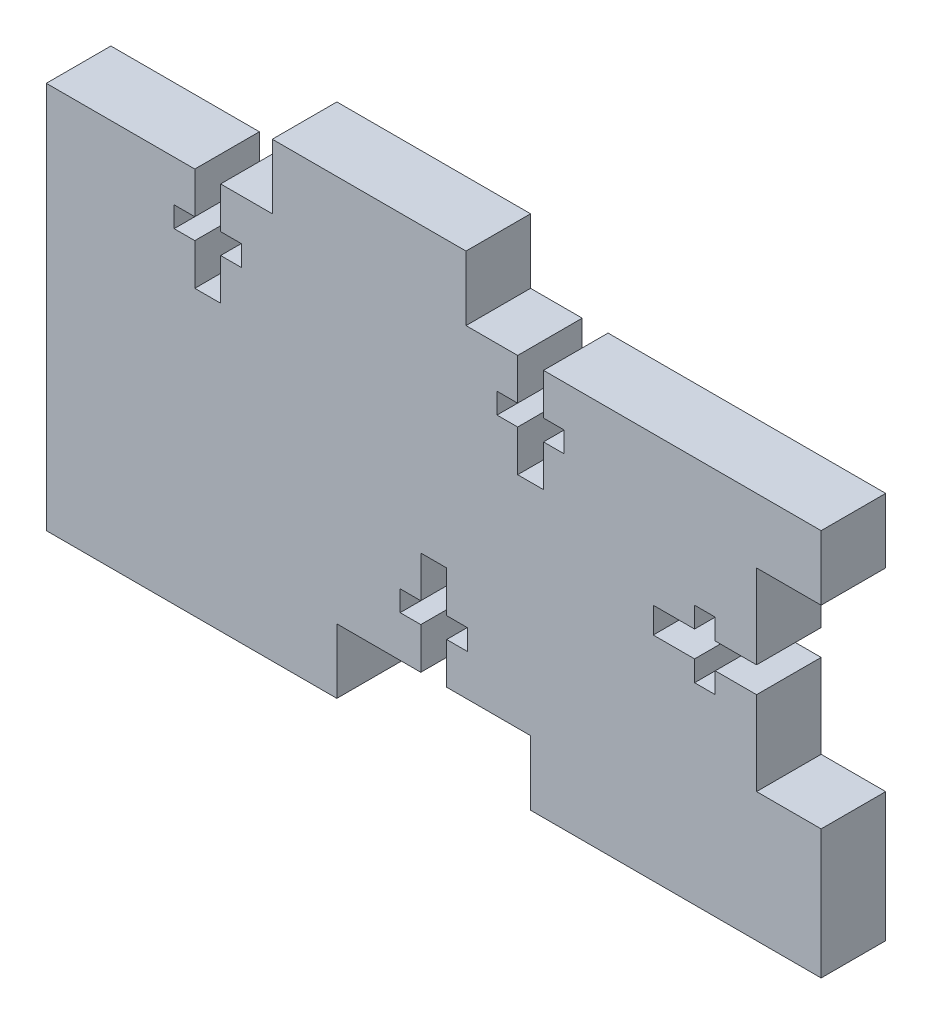
SolidWorks part; units mm, degrees
ref_plane "Front" through (0, 0, 0) normal (0, 0, 1) x (1, 0, 0)
ref_plane "Top" through (0, 0, 0) normal (0, 1, 0) x (1, 0, 0)
ref_plane "Right" through (0, 0, 0) normal (1, 0, 0) x (0, 0, -1)
sketch "Sketch1" plane through (0, 0, 0) normal (0, 0, 1) x (1, 0, 0)
  line L1 (-38.1, -15.875) -> (38.1, -15.875)
  line L2 (-38.1, -15.875) -> (-38.1, 15.875)
  line L3 (-38.1, 15.875) -> (38.1, 15.875)
  line L4 (38.1, -15.875) -> (38.1, 15.875)
  line L5 (-38.1, -15.875) -> (38.1, 15.875) construction
  line L6 (-38.1, 15.875) -> (38.1, -15.875) construction
  point P0 (0, 0)
  dimension "D1" = 31.75
  dimension "D2" = 76.2
extrude "Boss-Extrude1" add sketch "Sketch1" along normal blind 6.35
sketch "Sketch2" plane through (0, 0, 6.35) normal (0, 0, 1) x (1, 0, 0)
  line L0 (-38.1, 15.875) -> (-38.1, -15.875) construction
  line L1 (-15.875, 15.875) -> (3.175, 15.875)
  line L2 (-15.875, 15.875) -> (-15.875, 22.225)
  line L3 (-15.875, 22.225) -> (3.175, 22.225)
  line L4 (3.175, 15.875) -> (3.175, 22.225)
  line L5 (-15.875, 15.875) -> (3.175, 22.225) construction
  line L6 (-15.875, 22.225) -> (3.175, 15.875) construction
  line L7 (38.1, 15.875) -> (-38.1, 15.875) construction
  point P0 (-6.35, 19.05)
  dimension "D1" = 19.05
  dimension "D2" = 6.35
  dimension "D3" = 31.75
extrude "Boss-Extrude2" add sketch "Sketch2" against normal up to surface (6.35 mm away) up to face at (0, 0, 0)
sketch "Sketch3" plane through (0, 0, 6.35) normal (0, 0, 1) x (1, 0, 0)
  line L0 (-6.35, 22.225) -> (-6.35, 15.7879) construction
  line L1 (3.175, 22.225) -> (-15.875, 22.225) construction
  line L2 (-15.875, 19.05) -> (3.175, 19.05) construction
  line L3 (-15.875, 22.225) -> (-15.875, 15.875) construction
  line L4 (3.175, 15.875) -> (3.175, 22.225) construction
  line L5 (-20.955, 11.811) -> (-18.923, 11.811)
  line L6 (-23.495, 15.875) -> (-20.955, 15.875)
  line L7 (-23.495, 15.875) -> (-23.495, 11.811)
  line L8 (-23.495, 5.715) -> (-20.955, 5.715)
  line L9 (-20.955, 15.875) -> (-20.955, 11.811)
  line L10 (-23.495, 15.875) -> (-20.955, 5.715) construction
  line L11 (-23.495, 5.715) -> (-20.955, 15.875) construction
  line L12 (-25.527, 9.779) -> (-23.495, 9.779)
  line L13 (-25.527, 9.779) -> (-25.527, 11.811)
  line L14 (-25.527, 11.811) -> (-23.495, 11.811)
  line L15 (-18.923, 9.779) -> (-18.923, 11.811)
  line L16 (-25.527, 9.779) -> (-18.923, 11.811) construction
  line L17 (-25.527, 11.811) -> (-18.923, 9.779) construction
  line L18 (-20.955, 9.779) -> (-18.923, 9.779)
  line L19 (-23.495, 9.779) -> (-23.495, 5.715)
  line L20 (-20.955, 9.779) -> (-20.955, 5.715)
  line L21 (-15.875, 15.875) -> (-38.1, 15.875) construction
  line L22 (12.827, 11.811) -> (6.223, 9.779) construction
  line L23 (12.827, 9.779) -> (6.223, 11.811) construction
  line L24 (10.795, 5.715) -> (8.255, 15.875) construction
  line L25 (10.795, 15.875) -> (8.255, 5.715) construction
  line L26 (8.255, 9.779) -> (8.255, 5.715)
  line L27 (10.795, 9.779) -> (10.795, 5.715)
  line L28 (8.255, 9.779) -> (6.223, 9.779)
  line L29 (6.223, 9.779) -> (6.223, 11.811)
  line L30 (12.827, 11.811) -> (10.795, 11.811)
  line L31 (12.827, 9.779) -> (12.827, 11.811)
  line L32 (12.827, 9.779) -> (10.795, 9.779)
  line L33 (8.255, 15.875) -> (8.255, 11.811)
  line L34 (10.795, 5.715) -> (8.255, 5.715)
  line L35 (10.795, 15.875) -> (10.795, 11.811)
  line L36 (10.795, 15.875) -> (8.255, 15.875)
  line L37 (8.255, 11.811) -> (6.223, 11.811)
  point P10 (-22.225, 10.795)
  point P15 (-22.225, 10.795)
  point P38 (9.525, 10.795)
  dimension "D1" = 2.54
  dimension "D2" = 10.16
  dimension "D3" = 2.032
  dimension "D4" = 6.604
  dimension "D5" = 15.875
extrude "Cut-Extrude1" cut sketch "Sketch3" against normal up to surface (6.35 mm away) up to face at (0.3969, 9.525, 0)
sketch "Sketch4" plane through (0, 0, 6.35) normal (0, 0, 1) x (1, 0, 0)
  line L0 (38.1, -15.875) -> (38.1, 15.875) construction
  line L1 (38.1, 0) -> (-38.1, 0) construction
  line L3 (38.1, -15.875) -> (38.1, 15.875) construction
  line L4 (31.75, -9.525) -> (38.1, -9.525)
  line L5 (31.75, -9.525) -> (31.75, -1.27)
  line L6 (31.75, 9.525) -> (38.1, 9.525)
  line L7 (38.1, -9.525) -> (38.1, 9.525)
  line L8 (31.75, -9.525) -> (38.1, 9.525) construction
  line L9 (31.75, 9.525) -> (38.1, -9.525) construction
  line L10 (25.654, 1.27) -> (21.59, 1.27)
  line L11 (31.75, 1.27) -> (27.686, 1.27)
  line L12 (0, 0) -> (0, 22.225) construction
  line L13 (31.75, -1.27) -> (27.686, -1.27)
  line L14 (21.59, 1.27) -> (21.59, -1.27)
  line L15 (31.75, 1.27) -> (21.59, -1.27) construction
  line L16 (31.75, -1.27) -> (21.59, 1.27) construction
  line L17 (25.654, 3.302) -> (27.686, 3.302)
  line L18 (25.654, 3.302) -> (25.654, 1.27)
  line L19 (25.654, -3.302) -> (27.686, -3.302)
  line L20 (27.686, 3.302) -> (27.686, 1.27)
  line L21 (25.654, 3.302) -> (27.686, -3.302) construction
  line L22 (25.654, -3.302) -> (27.686, 3.302) construction
  line L23 (25.654, -1.27) -> (21.59, -1.27)
  line L24 (25.654, -1.27) -> (25.654, -3.302)
  line L25 (27.686, -1.27) -> (27.686, -3.302)
  line L26 (31.75, 1.27) -> (31.75, 9.525)
  line L27 (3.175, 22.225) -> (-15.875, 22.225) construction
  point P0 (38.1, 0)
  point P7 (34.925, 0)
  point P14 (26.67, 0)
  point P19 (26.67, 0)
  point P40 (-30.4006, -32.6246)
  dimension "D1" = 6.35
  dimension "D2" = 19.05
  dimension "D3" = 2.54
  dimension "D4" = 10.16
  dimension "D5" = 6.604
  dimension "D6" = 2.032
  dimension "D7" = 1.27
extrude "Cut-Extrude4" cut sketch "Sketch4" against normal up to surface (6.35 mm away) up to face at (-4.7427, 10.4775, 0)
sketch "Sketch5" plane through (0, 0, 6.35) normal (0, 0, 1) x (1, 0, 0)
  line L1 (-38.1, -15.875) -> (38.1, -15.875)
  line L2 (-38.1, -15.875) -> (-38.1, -22.225)
  line L3 (-38.1, -22.225) -> (38.1, -22.225)
  line L4 (38.1, -15.875) -> (38.1, -22.225)
  dimension "D1" = 6.35
extrude "Boss-Extrude3" add sketch "Sketch5" against normal up to surface (6.35 mm away) up to face at (6.4161, 6.985, 0)
sketch "Sketch6" plane through (0, 0, 6.35) normal (0, 0, 1) x (1, 0, 0)
  line L0 (-38.1, -22.225) -> (38.1, -22.225) construction
  line L1 (0, -22.225) -> (0, -1.6974) construction
  line L2 (-9.525, -22.225) -> (9.525, -22.225)
  line L3 (-9.525, -22.225) -> (-9.525, -15.875)
  line L4 (-9.525, -15.875) -> (-1.27, -15.875)
  line L5 (9.525, -22.225) -> (9.525, -15.875)
  line L6 (1.27, -15.875) -> (9.525, -15.875)
  line L7 (-1.27, -9.779) -> (-1.27, -5.715)
  line L8 (-1.27, -15.875) -> (-1.27, -11.811)
  line L9 (-1.27, -5.715) -> (1.27, -5.715)
  line L10 (1.27, -15.875) -> (1.27, -11.811)
  line L11 (-1.27, -15.875) -> (1.27, -5.715) construction
  line L12 (-1.27, -5.715) -> (1.27, -15.875) construction
  line L13 (-3.302, -11.811) -> (-1.27, -11.811)
  line L14 (-3.302, -11.811) -> (-3.302, -9.779)
  line L15 (-3.302, -9.779) -> (-1.27, -9.779)
  line L16 (3.302, -11.811) -> (3.302, -9.779)
  line L17 (-3.302, -11.811) -> (3.302, -9.779) construction
  line L18 (-3.302, -9.779) -> (3.302, -11.811) construction
  line L19 (1.27, -11.811) -> (3.302, -11.811)
  line L20 (1.27, -9.779) -> (1.27, -5.715)
  line L21 (1.27, -9.779) -> (3.302, -9.779)
  point P0 (0, -22.225)
  point P10 (0, -10.795)
  point P15 (0, -10.795)
  dimension "D1" = 19.05
  dimension "D2" = 6.35
  dimension "D3" = 9.525
  dimension "D4" = 10.16
  dimension "D5" = 2.54
  dimension "D6" = 2.032
  dimension "D7" = 6.604
extrude "Cut-Extrude5" cut sketch "Sketch6" against normal up to surface (6.35 mm away) up to face at (6.4161, 6.7204, 0)
